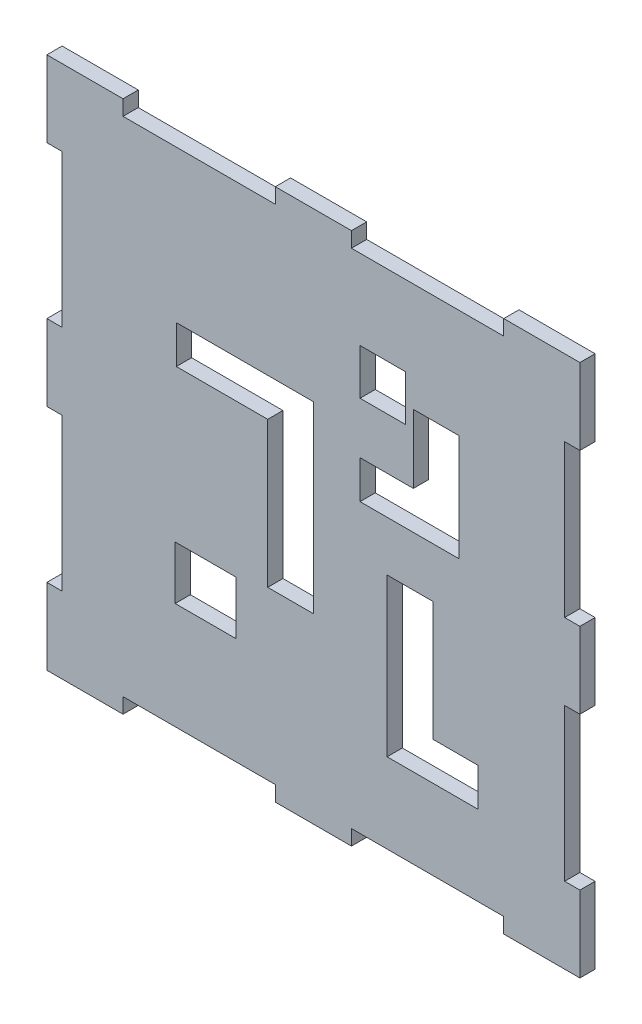
SolidWorks part; units mm, degrees
ref_plane "Front Plane" through (0, 0, 0) normal (0, 0, 1) x (1, 0, 0)
ref_plane "Top Plane" through (0, 0, 0) normal (0, 1, 0) x (1, 0, 0)
ref_plane "Right Plane" through (0, 0, 0) normal (1, 0, 0) x (0, 0, -1)
sketch "Sketch1" plane through (0, 0, 0) normal (0, 0, 1) x (1, 0, 0)
  line L1 (-35, -35) -> (35, -35)
  line L2 (-35, -35) -> (-35, 35)
  line L3 (-35, 35) -> (35, 35)
  line L4 (35, -35) -> (35, 35)
  line L5 (0, 35) -> (0, -35) construction
  line L6 (-35, 0) -> (35, 0) construction
  line L11 (0, 18) -> (0, -18) construction
  line L12 (-17.25, 0) -> (17.25, 0) construction
  point P0 (0, 0)
  point P4 (0, 0)
  dimension "D1" = 70
  dimension "D2" = 70
extrude "Boss-Extrude1" add sketch "Sketch1" against normal blind 2
sketch "Sketch2" plane through (0, 0, 0) normal (0, 0, 1) x (1, 0, 0)
  line L0 (-35, 35) -> (-25, 35)
  line L1 (35, 35) -> (-35, 35) construction
  line L2 (-25, 35) -> (-5, 35)
  line L3 (-5, 35) -> (5, 35)
  line L4 (5, 35) -> (25, 35)
  line L6 (35, 35) -> (35, 25)
  line L7 (-25, 33) -> (-5, 33)
  line L8 (-25, 33) -> (-25, 37)
  line L9 (-25, 37) -> (-5, 37)
  line L10 (-5, 33) -> (-5, 37)
  line L11 (-15, 37) -> (-15, 33) construction
  line L12 (-25, 35) -> (-5, 35) construction
  line L13 (5, 33) -> (25, 33)
  line L14 (5, 33) -> (5, 37)
  line L15 (5, 37) -> (25, 37)
  line L16 (25, 33) -> (25, 37)
  line L17 (15, 37) -> (15, 33) construction
  line L18 (5, 35) -> (25, 35) construction
  line L19 (35, -35) -> (35, 35) construction
  line L20 (35, 25) -> (35, 5)
  line L21 (35, 5) -> (35, -5)
  line L22 (35, -5) -> (35, -25)
  line L23 (-35, -35) -> (-25, -35)
  line L24 (35, -5) -> (33, -5)
  line L25 (35, -5) -> (35, -25)
  line L26 (35, -25) -> (33, -25)
  line L27 (33, -5) -> (33, -25)
  line L28 (35, 25) -> (33, 25)
  line L29 (35, 25) -> (35, 5)
  line L30 (35, 5) -> (33, 5)
  line L31 (33, 25) -> (33, 5)
  line L32 (-35, -35) -> (35, -35) construction
  line L33 (-25, -35) -> (-5, -35)
  line L34 (-5, -35) -> (5, -35)
  line L35 (5, -35) -> (25, -35)
  line L36 (-35, 35) -> (-35, 25)
  line L37 (-25, -35) -> (-5, -35)
  line L38 (-25, -35) -> (-25, -33)
  line L39 (-25, -33) -> (-5, -33)
  line L40 (-5, -35) -> (-5, -33)
  line L41 (5, -35) -> (25, -35)
  line L42 (5, -35) -> (5, -33)
  line L43 (5, -33) -> (25, -33)
  line L44 (25, -35) -> (25, -33)
  line L45 (-35, 35) -> (-35, -35) construction
  line L46 (-35, 25) -> (-35, 5)
  line L47 (-35, 5) -> (-35, -5)
  line L48 (-35, -5) -> (-35, -25)
  line L50 (-35, 25) -> (-33, 25)
  line L51 (-35, 25) -> (-35, 5)
  line L52 (-35, 5) -> (-33, 5)
  line L53 (-33, 25) -> (-33, 5)
  line L54 (-35, -5) -> (-33, -5)
  line L55 (-35, -5) -> (-35, -25)
  line L56 (-35, -25) -> (-33, -25)
  line L57 (-33, -5) -> (-33, -25)
  point P7 (15, 35)
  point P9 (-15, 35)
  point P10 (-15, 35)
  point P14 (15, 35)
  line M25 (35, -35) -> (35, 35)
  line M26 (35, 35) -> (-35, 35)
  line M27 (-35, 35) -> (-35, -35)
  line M28 (-35, -35) -> (35, -35)
  dimension "D1" = 10
  dimension "D2" = 20
  dimension "D3" = 10
  dimension "D4" = 20
  dimension "D5" = 4
  dimension "D6" = 20
  dimension "D7" = 20
  dimension "D8" = 4
  dimension "D9" = 10
  dimension "D10" = 20
  dimension "D11" = 10
  dimension "D12" = 20
  dimension "D13" = 2
  dimension "D14" = 2
  dimension "D15" = 10
  dimension "D16" = 20
  dimension "D17" = 10
  dimension "D18" = 20
  dimension "D19" = 20
  dimension "D20" = 20
  dimension "D21" = 2
  dimension "D22" = 2
  dimension "D23" = 10
  dimension "D24" = 20
  dimension "D25" = 10
  dimension "D26" = 20
  dimension "D27" = 2
  dimension "D28" = 2
extrude "Cut-Extrude1" cut sketch "Sketch2" against normal blind 2 contours L53 L50 L52 M27 | L57 L54 L56 M27 | L40 L39 L38 M28 | L44 L43 L42 M28 | L24 L27 L26 M25 | L28 L31 L30 M25 | L13 L16 L14 M26 | L7 L10 L8 M26
sketch "Sketch3" plane through (0, 0, 0) normal (0, 0, 1) x (1, 0, 0)
  line L0 (0, 0) -> (-6, 0)
  line L1 (0, 0) -> (0, -11.0671)
  line L2 (0, -11.0671) -> (-6, -11.0671)
  line L3 (-6, 0) -> (-6, -11.0671)
  line L4 (0, 0) -> (-6, 0)
  line L5 (0, 0) -> (0, 13.0448)
  line L6 (0, 13.0448) -> (-6, 13.0448)
  line L7 (-6, 0) -> (-6, 13.0448)
  line L8 (-6, 13.0448) -> (-18, 13.0448)
  line L9 (-6, 13.0448) -> (-6, 8.0448)
  line L10 (-6, 8.0448) -> (-18, 8.0448)
  line L11 (-18, 13.0448) -> (-18, 8.0448)
  line L12 (0, -11.0671) -> (0, -6.3585)
  line L14 (15.6811, -12.8211) -> (9.6811, -12.8211)
  line L15 (15.6811, -12.8211) -> (15.6811, -1.8211)
  line L16 (15.6811, -1.8211) -> (9.6811, -1.8211)
  line L17 (9.6811, -12.8211) -> (9.6811, -1.8211)
  line L18 (13.127, 18.7436) -> (19.127, 18.7436)
  line L19 (13.127, 18.7436) -> (13.127, 4.7436)
  line L20 (13.127, 4.7436) -> (19.127, 4.7436)
  line L21 (19.127, 18.7436) -> (19.127, 4.7436)
  line L22 (-18.1545, -11.9858) -> (-10.1545, -11.9858)
  line L23 (-18.1545, -11.9858) -> (-18.1545, -18.9858)
  line L24 (-18.1545, -18.9858) -> (-10.1545, -18.9858)
  line L25 (-10.1545, -11.9858) -> (-10.1545, -18.9858)
  line L26 (6.127, 22.5) -> (12.127, 22.5)
  line L27 (6.127, 22.5) -> (6.127, 16.5)
  line L28 (6.127, 16.5) -> (12.127, 16.5)
  line L29 (12.127, 22.5) -> (12.127, 16.5)
  line L30 (9.6811, -12.8211) -> (15.6811, -12.8211)
  line L31 (9.6811, -12.8211) -> (9.6811, -22.5)
  line L32 (9.6811, -22.5) -> (15.6811, -22.5)
  line L33 (15.6811, -12.8211) -> (15.6811, -22.5)
  line L34 (15.6811, -22.5) -> (21.5929, -22.5)
  line L35 (15.6811, -22.5) -> (15.6811, -17.5)
  line L36 (15.6811, -17.5) -> (21.5929, -17.5)
  line L37 (21.5929, -22.5) -> (21.5929, -17.5)
  line L38 (-22.5, -22.5) -> (22.5, -22.5)
  line L39 (-22.5, -22.5) -> (-22.5, 22.5)
  line L40 (-22.5, 22.5) -> (22.5, 22.5)
  line L41 (22.5, -22.5) -> (22.5, 22.5)
  line L42 (0, 22.5) -> (0, -22.5) construction
  line L43 (-22.5, 0) -> (22.5, 0) construction
  line L44 (13.127, 4.7436) -> (6.127, 4.7436)
  line L45 (13.127, 4.7436) -> (13.127, 9.7436)
  line L46 (13.127, 9.7436) -> (6.127, 9.7436)
  line L47 (6.127, 4.7436) -> (6.127, 9.7436)
  line L48 (9.6811, -12.8211) -> (15.6811, -12.8211)
  line L49 (9.6811, -12.8211) -> (9.6811, -22.5)
  line L50 (9.6811, -22.5) -> (15.6811, -22.5)
  line L51 (15.6811, -12.8211) -> (15.6811, -22.5)
  point P11 (0, 0)
  point P43 (0, 0)
  dimension "D1" = 45
  dimension "D2" = 4.5
  dimension "D3" = 6.127
  dimension "D4" = 6
  dimension "D5" = 14
  dimension "D6" = 7
  dimension "D7" = 3.7564
  dimension "D8" = 6.5647
  dimension "D9" = 11
  dimension "D10" = 9.6789
  dimension "D11" = 5.9118
  dimension "D12" = 7
  dimension "D13" = 8
  dimension "D14" = 4.1545
  dimension "D15" = 7
  dimension "D16" = 19.1119
  dimension "D17" = 5
  dimension "D18" = 12
  dimension "D19" = 6
  dimension "D20" = 5
  dimension "D21" = 6
  dimension "D22" = 1
extrude "Cut-Extrude2" cut sketch "Sketch3" against normal blind 10 contours L21 L18 L19 L20 | L47 L44 L19 L46 | L29 L26 L27 L28 | L17 L14 L15 L16 | L33 L14 L31 L32 | L34 L37 L36 L33 | L25 L22 L23 L24 | L0 L3 L2 L1 | L7 L0 L5 L6 | L8 L11 L10 L7
